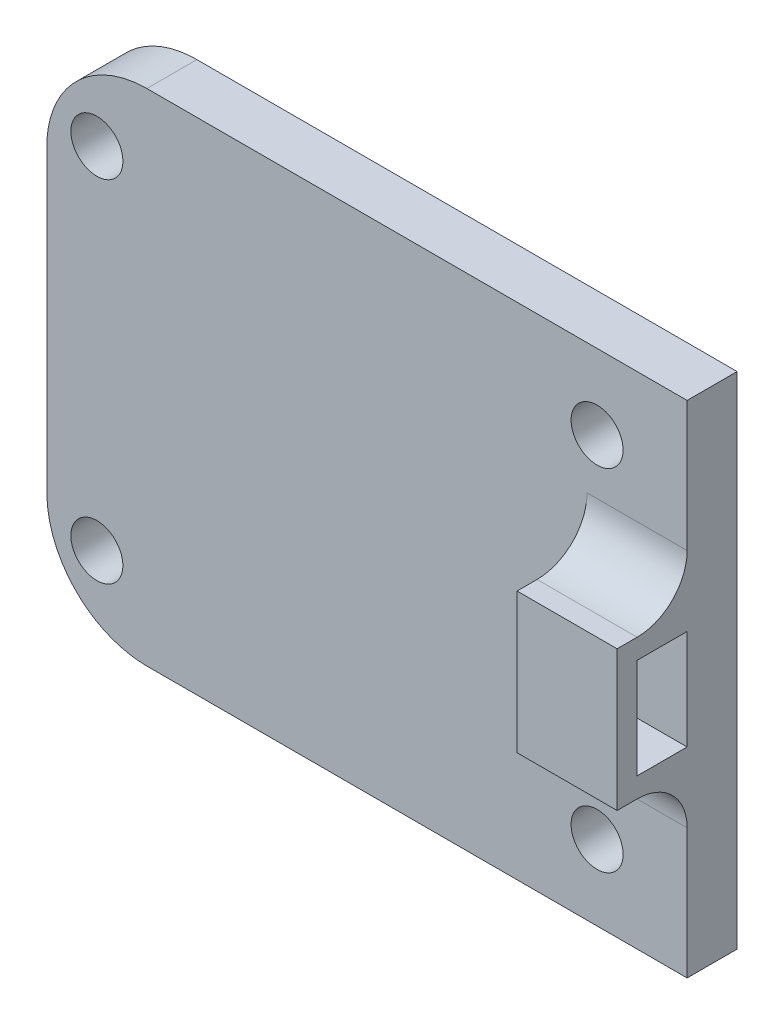
SolidWorks part; units mm, degrees
ref_plane "Front Plane" through (0, 0, 0) normal (0, 0, 1) x (1, 0, 0)
ref_plane "Top Plane" through (0, 0, 0) normal (0, 1, 0) x (1, 0, 0)
ref_plane "Right Plane" through (0, 0, 0) normal (1, 0, 0) x (0, 0, -1)
sketch "Sketch1" plane through (0, 0, 0) normal (0, 0, 1) x (1, 0, 0)
  line L1 (0, 0) -> (64, 0)
  line L2 (0, 0) -> (0, 50)
  line L3 (0, 50) -> (64, 50)
  line L4 (64, 0) -> (64, 50)
  circle A0 centre (5, 42.5) radius 2.6
  circle A1 centre (55, 42.5) radius 2.6
  circle A2 centre (55, 7.5) radius 2.6
  circle A3 centre (5, 7.5) radius 2.6
  dimension "D3" = 5.2
  dimension "D4" = 5
  dimension "D5" = 7.5
  dimension "D1" = 64
  dimension "D2" = 50
  dimension "D6" = 2
  dimension "D7" = 2
extrude "Boss-Extrude1" add sketch "Sketch1" along normal blind 5
fillet "Fillet1" radius 10 2 edges at (0, 50, 2.5) (0, 0, 2.5)
sketch "Sketch3" plane through (64, 0, 0) normal (1, 0, 0) x (0, 0, -1)
  line L0 (-5, 0) -> (-5, 50) construction
  line L1 (-5, 30) -> (-10, 30)
  line L3 (-5, 20) -> (-10, 20)
  line L4 (-10, 30) -> (-10, 20)
  line L5 (-12, 32) -> (-12, 18)
  line L6 (-5, 18) -> (-12, 18)
  line L8 (-5, 32) -> (-12, 32)
  line L9 (-5, 18) -> (-5, 20)
  line L10 (-5, 30) -> (-5, 32)
  line L11 (-3, 32) -> (-3, 18) construction
  line L12 (-3, 32) -> (-12, 32) construction
  line L13 (-3, 18) -> (-12, 18) construction
  line L14 (-5, 30) -> (-5, 20) construction
  line L15 (-5, 0) -> (0, 0) construction
  point P14 (-2.5, 0)
  dimension "D1" = 5
  dimension "D2" = 10
  dimension "D4" = 18
  dimension "D3" = 2
extrude "Boss-Extrude2" add sketch "Sketch3" against normal blind 10
fillet "Fillet2" radius 5 2 edges at (59, 32, 5) (59, 18, 5)
